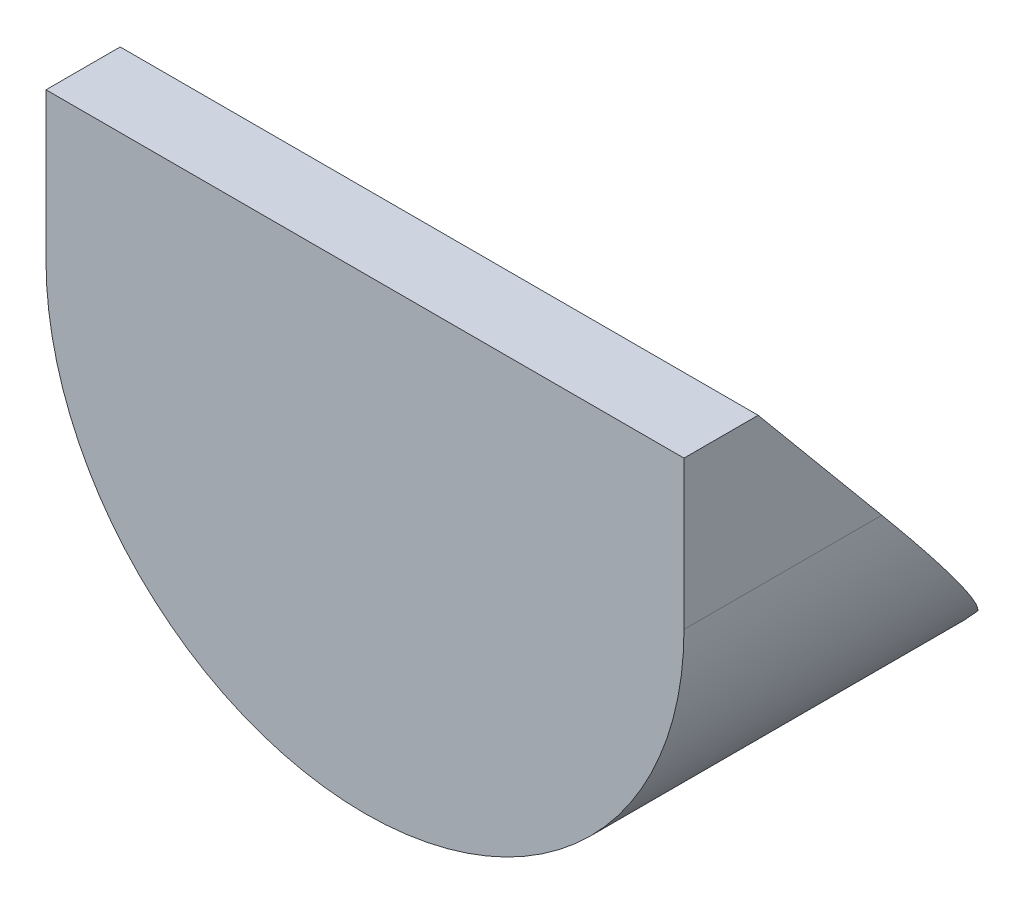
SolidWorks part; units mm, degrees
ref_plane "Спереди" through (0, 0, 0) normal (0, 0, 1) x (1, 0, 0)
ref_plane "Сверху" through (0, 0, 0) normal (0, 1, 0) x (1, 0, 0)
ref_plane "Справа" through (0, 0, 0) normal (1, 0, 0) x (0, 0, -1)
sketch "Эскиз1" plane through (0, 0, 0) normal (0, 0, 1) x (1, 0, 0)
  line L0 (0, 20) -> (0, 0)
  line L1 (86, 0) -> (86, 20)
  line L2 (86, 20) -> (0, 20)
  arc A0 (0, 0) -> (86, 0) centre (43, 0) ccw
  dimension "D1" = 86
  dimension "D2" = 20
extrude "Бобышка-Вытянуть1" add sketch "Эскиз1" along normal blind 50
sketch "Эскиз2" plane through (0, 0, 0) normal (1, 0, 0) x (0, 0, -1)
  line L0 (-40, 20) -> (0, -28)
  line L1 (-50, 20) -> (0, 20) construction
  line L2 (0, -43) -> (0, 0) construction
  line L3 (0, -28) -> (0, 20)
  line L4 (0, 20) -> (-40, 20)
  line L5 (-50, 0) -> (-50, 20) construction
  line L6 (-50, -43) -> (0, -43) construction
  dimension "D1" = 10
  dimension "D2" = 15
extrude "Вырез-Вытянуть1" cut sketch "Эскиз2" against normal through all and the other way through all
ref_plane "Плоскость1" through (0, -43, 0) normal (0, -1, 0) x (-1, 0, 0)
sketch "Эскиз3" plane through (0, -43, 0) normal (0, -1, 0) x (-1, 0, 0)
  line L0 (-43, -50) -> (-43, -38) construction
  line L1 (-86, -50) -> (0, -50) construction
  circle A0 centre (-43, -38) radius 2
  dimension "D1" = 4
  dimension "D2" = 12
extrude "Вырез-Вытянуть2" cut sketch "Эскиз3" against normal blind 20
